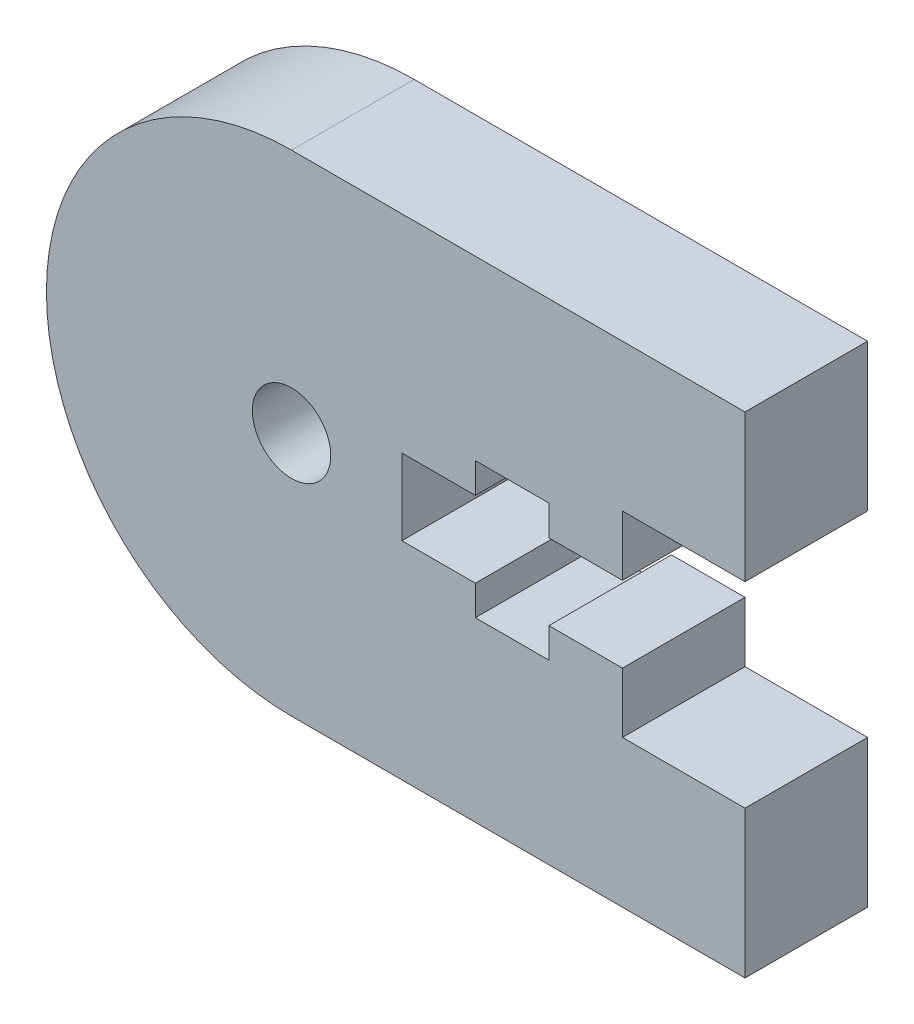
SolidWorks part; units mm, degrees
ref_plane "Plan de face" through (0, 0, 0) normal (0, 0, 1) x (1, 0, 0)
ref_plane "Plan de dessus" through (0, 0, 0) normal (0, 1, 0) x (1, 0, 0)
ref_plane "Plan de droite" through (0, 0, 0) normal (1, 0, 0) x (0, 0, -1)
ref_plane "Plan1" through (0, 0, 0) normal (0, 0, -1) x (-1, 0, 0)
sketch "Esquisse1" plane through (0, 0, 0) normal (0, 0, -1) x (-1, 0, 0)
  line L0 (-17, 10) -> (-17, -10)
  line L1 (-17, -10) -> (1.5, -10)
  line L2 (1.5, 10) -> (-17, 10)
  arc A0 (1.5, -10) -> (1.5, 10) centre (1.5, 0) ccw
  dimension "D1" = 20
extrude "Boss.-Extru.1" add sketch "Esquisse1" against normal blind 5
sketch "Esquisse2" plane through (0, 0, 5) normal (0, 0, 1) x (1, 0, 0)
  line L0 (17, -4) -> (17, 4)
  line L1 (17, 4) -> (12, 4)
  line L2 (12, 4) -> (12, -4)
  line L3 (12, -4) -> (17, -4)
extrude "Enlèv. mat.-Extru.1" cut sketch "Esquisse2" against normal through all
sketch "Esquisse3" plane through (0, 0, 5) normal (0, 0, 1) x (1, 0, 0)
  line L0 (-10.1603, -5) -> (7, -5)
  line L1 (7, -5) -> (7, 5)
  line L2 (7, 5) -> (-10.1603, 5)
  arc A0 (-10.1603, 5) -> (-10.1603, -5) centre (-1.5, 0) ccw
extrude "Enlèv. mat.-Extru.2" cut sketch "Esquisse3" against normal blind 2.5
hole_wizard "Diamètre du perçage Ø2.5 (2.5)2" positions "Esquisse7" profile "Esquisse6" hole size "Ø2.5" standard "Ansi Metric"
sketch "Esquisse7" plane through (0, 0, 2.5) normal (0, 0, 1) x (1, 0, 0)
  point P0 (-1.5, 0)
sketch "Esquisse6" plane through (-1.5, 0, 2.5) normal (1, 0, 0) x (0, -1, 0)
  line L0 (0, 0) -> (0, 2.5)
  line L1 (0, 2.5) -> (1.25, 2.5)
  line L2 (1.25, 2.5) -> (1.25, 0)
  line L5 (1.25, 0) -> (0, 0)
  line L11 (0, -6.35) -> (0, 107.95) construction
  dimension "Diamètre du perçage jusqu'au prochain" = 2.5
  dimension "Profondeur du perçage jusqu'au prochain" = 2.5
sketch "Esquisse9" plane through (0, 0, 5) normal (0, 0, 1) x (1, 0, 0)
  line L0 (-1.5, 10) -> (17, 10) construction
  line L1 (-1.5, -10) -> (7.75, -10)
  line L2 (-1.5, -10) -> (-1.5, 10)
  line L3 (-1.5, 10) -> (7.75, 10)
  line L4 (7.75, -10) -> (7.75, 10)
  arc A0 (-1.5, -10) -> (-1.5, 10) centre (-1.5, 0) cw
  line M2 (-10.1603, 5) -> (7, 5)
  line M3 (7, 5) -> (7, -5)
  line M4 (7, -5) -> (-10.1603, -5)
extrude "Boss.-Extru.2" add sketch "Esquisse9" against normal blind 5 contours A0 L2 M4 M2 | L2 M4 M3 M2
sketch "Esquisse10" plane through (0, 0, 5) normal (0, 0, 1) x (1, 0, 0)
  line L0 (12, 4) -> (12, -4) construction
  line L1 (17, 4) -> (12, 4) construction
  line L2 (12, -1.55) -> (3, -1.55)
  line L3 (12, -1.55) -> (12, 1.55)
  line L4 (12, 1.55) -> (3, 1.55)
  line L5 (3, -1.55) -> (3, 1.55)
  line L6 (6, -2.77) -> (9, -2.77)
  line L7 (6, -2.77) -> (6, 2.78)
  line L8 (6, 2.78) -> (9, 2.78)
  line L9 (9, -2.77) -> (9, 2.78)
  line L10 (-1.5, 10) -> (-1.5, -10) construction
  circle A0 centre (-1.5, 0) radius 1.6
  line M12 (12, -4) -> (12, 4)
  dimension "D8" = 3.2
  dimension "D1" = 3
  dimension "D2" = 3
  dimension "D3" = 2.45
  dimension "D4" = 3.1
  dimension "D5" = 5.55
  dimension "D6" = 1.23
  dimension "D7" = 3
extrude "Enlèv. mat.-Extru.3" cut sketch "Esquisse10" against normal through all contours L2 L9 L4 L7 | L6 L9 L2 L7 | L2 L7 L4 L5 | L4 L9 L8 L7 | L9 L2 L4 M12 | L10 A0 | A0 L10
chamfer "Chanfrein1" distance 2 angle 45 1 edges at (0.1, 0, 0)
